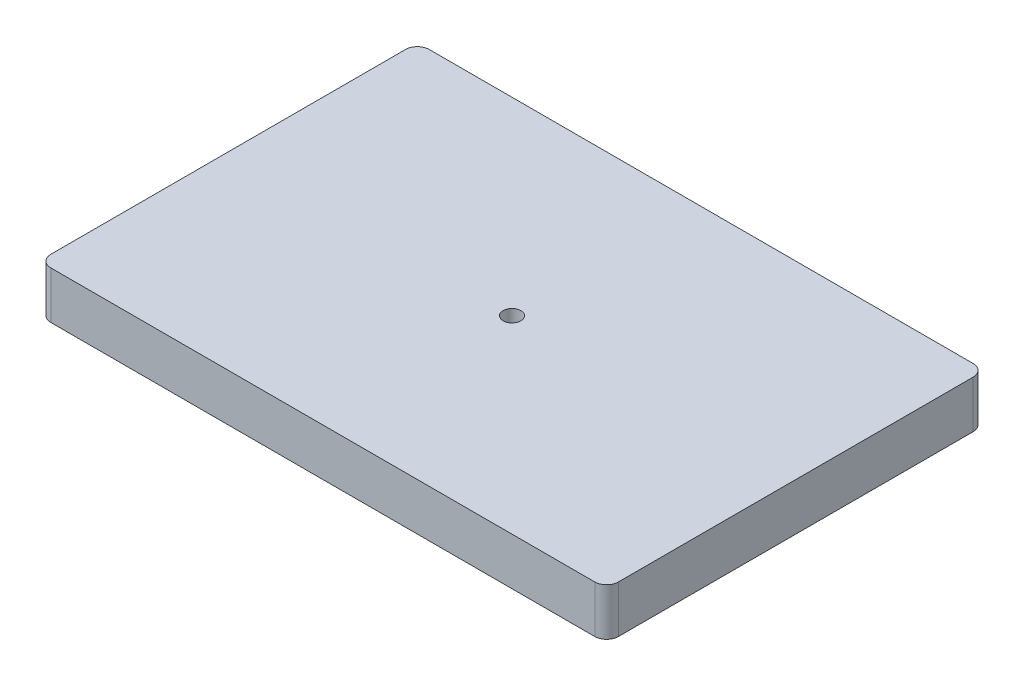
SolidWorks part; units mm, degrees
ref_plane "Front Plane" through (0, 0, 0) normal (0, 0, 1) x (1, 0, 0)
ref_plane "Top Plane" through (0, 0, 0) normal (0, 1, 0) x (1, 0, 0)
ref_plane "Right Plane" through (0, 0, 0) normal (1, 0, 0) x (0, 0, -1)
sketch "Sketch1" plane through (0, 0, 0) normal (0, 1, 0) x (1, 0, 0)
  line L1 (-73.025, 50.8) -> (73.025, 50.8)
  line L2 (-76.2, 47.625) -> (-76.2, -47.625)
  line L3 (-73.025, -50.8) -> (73.025, -50.8)
  line L4 (76.2, 47.625) -> (76.2, -47.625)
  line L5 (-76.2, 50.8) -> (76.2, -50.8) construction
  line L6 (-76.2, -50.8) -> (76.2, 50.8) construction
  arc A0 (-73.025, -50.8) -> (-76.2, -47.625) centre (-73.025, -47.625) cw
  arc A1 (73.025, -50.8) -> (76.2, -47.625) centre (73.025, -47.625) ccw
  arc A2 (76.2, 47.625) -> (73.025, 50.8) centre (73.025, 47.625) ccw
  arc A3 (-73.025, 50.8) -> (-76.2, 47.625) centre (-73.025, 47.625) ccw
  point P0 (0, 0)
  dimension "D3" = 3.175
  dimension "D1" = 152.4
  dimension "D2" = 101.6
extrude "Boss-Extrude1" add sketch "Sketch1" along normal blind 12.7
sketch "Sketch2" plane through (0, 0, 0) normal (0, 1, 0) x (1, 0, 0)
  circle A0 centre (0, 0) radius 2.3813
  dimension "D1" = 4.7625
extrude "Cut-Extrude1" cut sketch "Sketch2" against normal through all from surface at 12.7 starting at face at (0, 12.7, 0)
